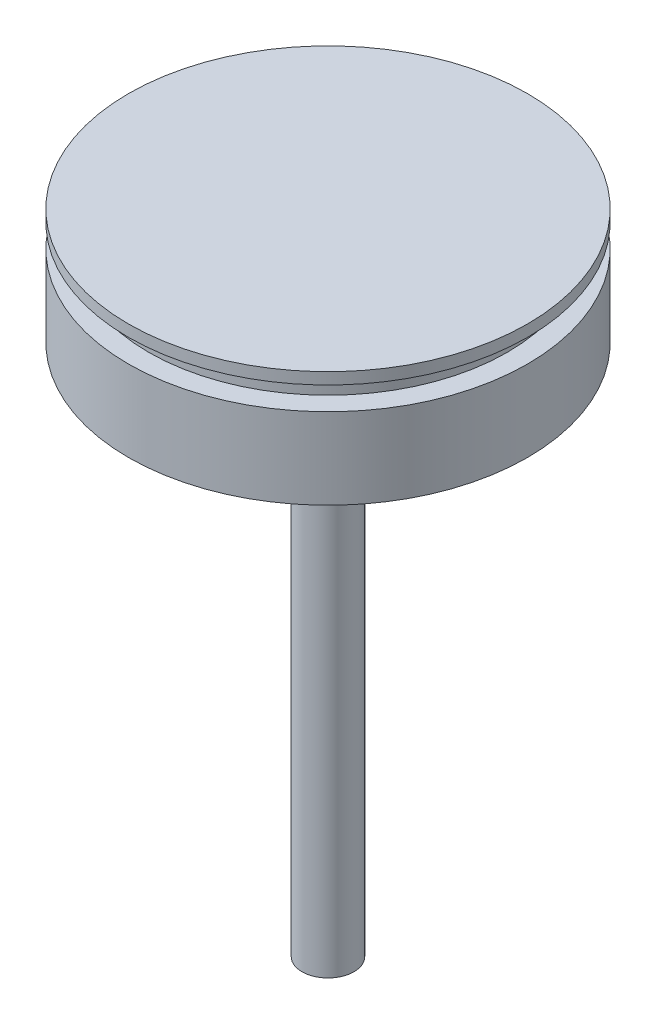
SolidWorks part; units mm, degrees
material "1023 Carbon Steel Sheet (SS)"
ref_plane "Front Plane" through (0, 0, 0) normal (0, 0, 1) x (1, 0, 0)
ref_plane "Top Plane" through (0, 0, 0) normal (0, 1, 0) x (1, 0, 0)
ref_plane "Right Plane" through (0, 0, 0) normal (1, 0, 0) x (0, 0, -1)
sketch "Sketch1" plane through (0, 0, 0) normal (1, 0, 0) x (0, 0, -1)
  line L0 (0, 0) -> (34.5, 0)
  line L1 (34.5, 0) -> (34.5, -2)
  line L2 (34.5, -2) -> (31, -2)
  line L3 (31, -2) -> (31, -6)
  line L4 (31, -6) -> (34.5, -6)
  line L5 (34.5, -20) -> (34.5, -18)
  line L6 (0, -20) -> (34.5, -20)
  line L7 (34.5, -18) -> (34.5, -14)
  line L17 (34.5, -14) -> (34.5, -6)
  line L18 (0, -20) -> (0, 0)
revolve "Revolve1" add sketch "Sketch1" angle 360 about L18
sketch "Sketch2" plane through (0, -20, 0) normal (0, -1, 0) x (1, 0, 0)
  circle A0 centre (0, 0) radius 4.5
extrude "Boss-Extrude1" add sketch "Sketch2" along normal blind 92
